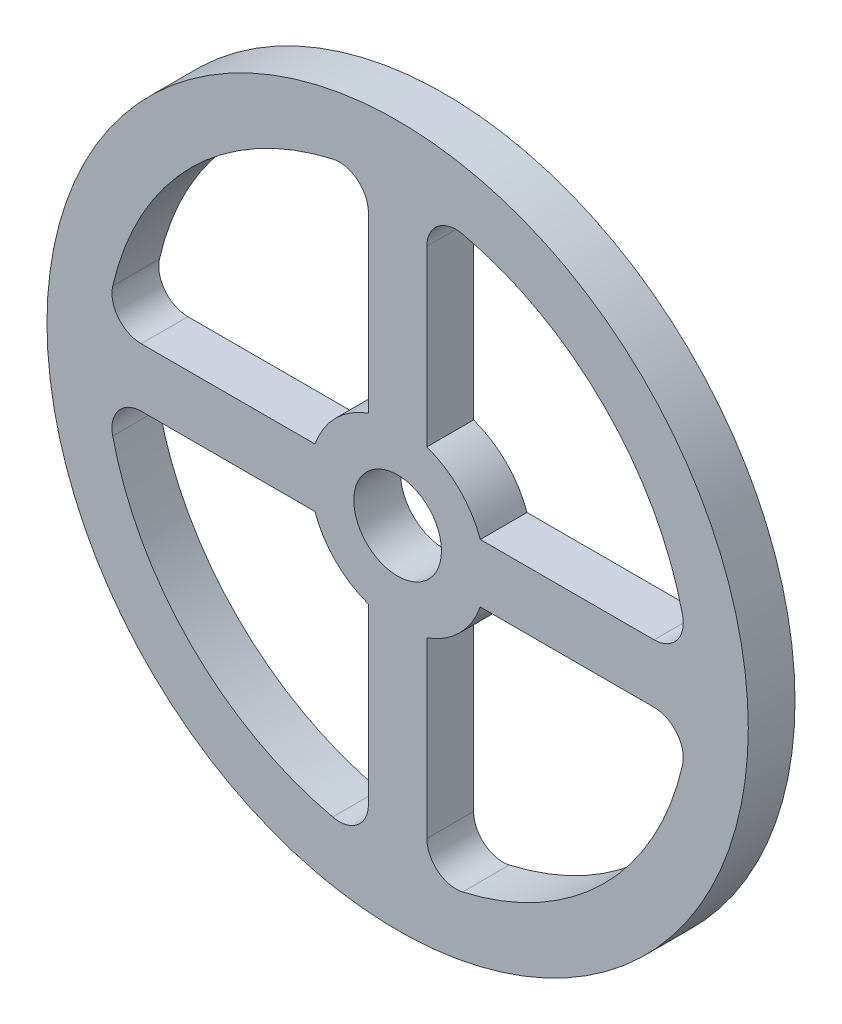
SolidWorks part; units mm, degrees
ref_plane "Front Plane" through (0, 0, 0) normal (0, 0, 1) x (1, 0, 0)
ref_plane "Top Plane" through (0, 0, 0) normal (0, 1, 0) x (1, 0, 0)
ref_plane "Right Plane" through (0, 0, 0) normal (1, 0, 0) x (0, 0, -1)
sketch "Sketch1" plane through (0, 0, 0) normal (0, 0, 1) x (1, 0, 0)
  line L0 (326.4568, 953.3242) -> (3554.6104, 953.3242) construction
  line L1 (-257.3134, 131.7374) -> (-187.3134, 131.7374) construction
  line L2 (-157.3134, 231.7374) -> (-157.3134, 161.7374) construction
  line L3 (-167.3134, 103.4531) -> (-167.3134, 43.9877)
  line L4 (-245.0631, 121.7374) -> (-185.5977, 121.7374)
  line L5 (-245.0631, 141.7374) -> (-185.5977, 141.7374)
  line L6 (-167.3134, 219.487) -> (-167.3134, 160.0217)
  line L7 (-147.3134, 219.487) -> (-147.3134, 160.0217)
  line L8 (-157.3134, 101.7374) -> (-157.3134, 31.7374) construction
  line L9 (-147.3134, 103.4531) -> (-147.3134, 43.9877)
  line L10 (-127.3134, 131.7374) -> (-57.3134, 131.7374) construction
  line L11 (-129.0291, 121.7374) -> (-69.5638, 121.7374)
  line L12 (-129.0291, 141.7374) -> (-69.5638, 141.7374)
  circle A0 centre (-157.3134, 131.7374) radius 120
  arc A1 (-179.5356, 229.237) -> (-254.813, 153.9596) centre (-157.3134, 131.7374) ccw
  arc A2 (-185.5977, 121.7374) -> (-167.3134, 103.4531) centre (-157.3134, 131.7374) ccw
  circle A3 centre (-157.3134, 131.7374) radius 15
  arc A4 (-254.813, 109.5152) -> (-179.5356, 34.2378) centre (-157.3134, 131.7374) ccw
  arc A5 (-59.8138, 153.9596) -> (-135.0912, 229.237) centre (-157.3134, 131.7374) ccw
  arc A6 (-135.0912, 34.2378) -> (-59.8138, 109.5152) centre (-157.3134, 131.7374) ccw
  arc A7 (-245.0631, 141.7374) -> (-254.813, 153.9596) centre (-245.0631, 151.7374) cw
  arc A8 (-245.0631, 121.7374) -> (-254.813, 109.5152) centre (-245.0631, 111.7374) ccw
  arc A9 (-179.5356, 34.2378) -> (-167.3134, 43.9877) centre (-177.3134, 43.9877) ccw
  arc A10 (-135.0912, 34.2378) -> (-147.3134, 43.9877) centre (-137.3134, 43.9877) cw
  arc A11 (-59.8138, 109.5152) -> (-69.5638, 121.7374) centre (-69.5638, 111.7374) ccw
  arc A12 (-59.8138, 153.9596) -> (-69.5638, 141.7374) centre (-69.5638, 151.7374) cw
  arc A13 (-147.3134, 219.487) -> (-135.0912, 229.237) centre (-137.3134, 219.487) cw
  arc A14 (-167.3134, 219.487) -> (-179.5356, 229.237) centre (-177.3134, 219.487) ccw
  arc A15 (-167.3134, 160.0217) -> (-185.5977, 141.7374) centre (-157.3134, 131.7374) ccw
  arc A16 (-129.0291, 141.7374) -> (-147.3134, 160.0217) centre (-157.3134, 131.7374) ccw
  arc A17 (-147.3134, 103.4531) -> (-129.0291, 121.7374) centre (-157.3134, 131.7374) ccw
  point P34 (-256.8122, 121.7374)
  point P37 (-167.3134, 32.2386)
  point P40 (-147.3134, 32.2386)
  point P43 (-57.8147, 121.7374)
  point P46 (-57.8147, 141.7374)
  dimension "D1" = 240
  dimension "D2" = 200
  dimension "D3" = 60
  dimension "D4" = 30
  dimension "D9" = 10
  dimension "D5" = 10
  dimension "D6" = 20
  dimension "D7" = 10
  dimension "D8" = 20
extrude "Boss-Extrude1" add sketch "Sketch1" along normal blind 16
